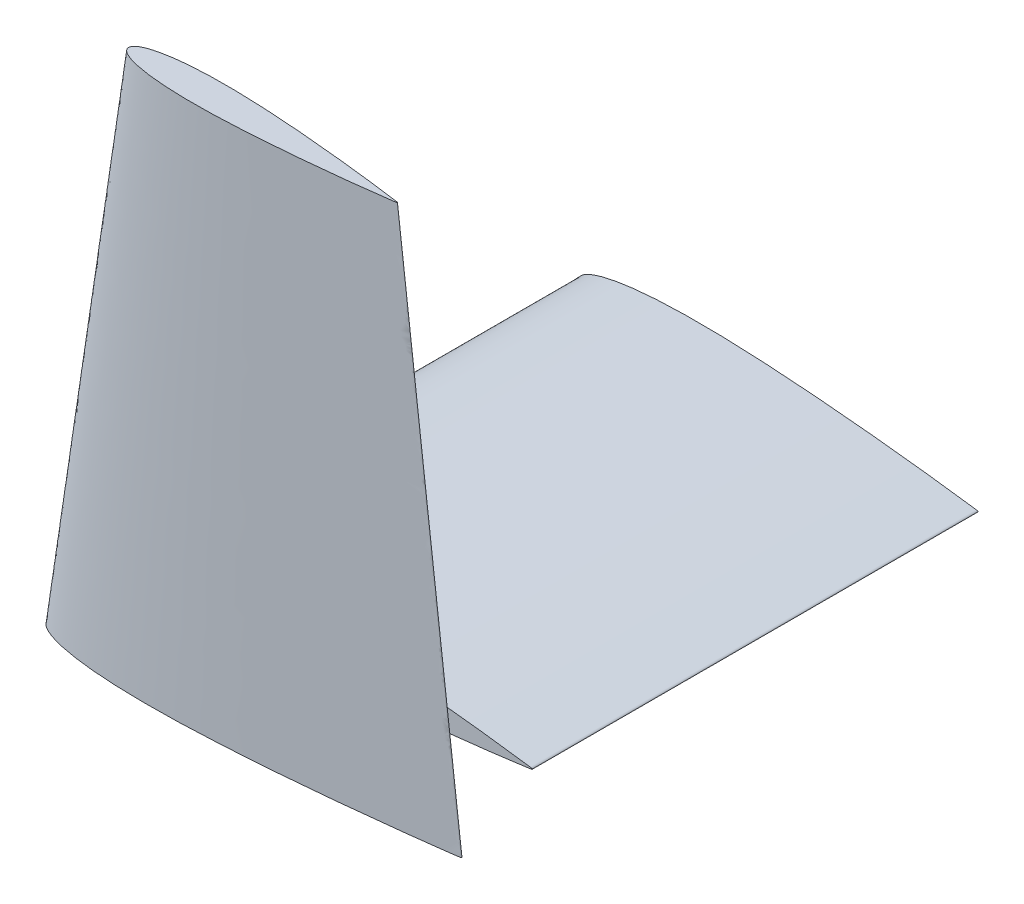
SolidWorks part; units mm, degrees
ref_plane "Front Plane" through (0, 0, 0) normal (0, 0, 1) x (1, 0, 0)
ref_plane "Top Plane" through (0, 0, 0) normal (0, 1, 0) x (1, 0, 0)
ref_plane "Right Plane" through (0, 0, 0) normal (1, 0, 0) x (0, 0, -1)
ref_plane "Plane1" through (0, 0, -61.341) normal (0, 0, 1) x (1, 0, 0)
sketch "Sketch2" plane through (0, 0, -61.341) normal (0, 0, 1) x (1, 0, 0)
  spline S1 degree 3 poles (318.9616, -0.5388) (318.9616, 0.5388) (317.8871, 0.4072) (316.5257, 0.7904) (314.029, 1.0273) (310.6656, 1.5357) (306.333, 2.103) (301.1081, 2.8022) (295.0047, 3.5926) (288.0667, 4.4725) (280.3349, 5.4267) (271.8575, 6.4421) (262.6867, 7.5062) (252.8789, 8.6045) (242.4947, 9.7236) (231.5982, 10.8496) (220.2564, 11.9679) (208.5394, 13.0629) (196.5193, 14.1202) (184.2704, 15.122) (171.8679, 16.0521) (159.3884, 16.8933) (146.9087, 17.6278) (134.5058, 18.2372) (122.2562, 18.7052) (110.2351, 19.0165) (98.5168, 19.156) (87.1732, 19.1125) (76.2743, 18.8777) (65.8873, 18.4456) (56.076, 17.8151) (46.9007, 16.9881) (38.4176, 15.971) (30.6784, 14.7725) (23.73, 13.4051) (17.6131, 11.8842) (12.3624, 10.2248) (8.0047, 8.4423) (4.5539, 6.5486) (2.0152, 4.5401) (0.3892, 2.3682) (-0.1814, 0) (0.3892, -2.3682) (2.0152, -4.5401) (4.5539, -6.5486) (8.0047, -8.4423) (12.3624, -10.2248) (17.6131, -11.8842) (23.73, -13.4051) (30.6784, -14.7725) (38.4176, -15.971) (46.9007, -16.9881) (56.076, -17.8151) (65.8873, -18.4456) (76.2743, -18.8777) (87.1732, -19.1125) (98.5168, -19.156) (110.2351, -19.0165) (122.2562, -18.7052) (134.5058, -18.2372) (146.9087, -17.6278) (159.3884, -16.8933) (171.8679, -16.0521) (184.2704, -15.122) (196.5193, -14.1202) (208.5394, -13.0629) (220.2564, -11.9679) (231.5982, -10.8496) (242.4947, -9.7236) (252.8789, -8.6045) (262.6867, -7.5062) (271.8575, -6.4421) (280.3349, -5.4267) (288.0667, -4.4725) (295.0047, -3.5926) (301.1081, -2.8022) (306.333, -2.103) (310.6656, -1.5357) (314.029, -1.0273) (316.5257, -0.7904) (317.8871, -0.4072) (318.9616, -0.5388) (318.9616, 0.5388) (317.8871, 0.4072) knots -0.004279 -0.001997 -0.001234 0 0.000762 0.003045 0.006832 0.012101 0.018818 0.026939 0.036415 0.047185 0.05918 0.072328 0.086544 0.101741 0.117823 0.134691 0.15224 0.170361 0.188941 0.207865 0.227016 0.246276 0.265525 0.284645 0.30352 0.322035 0.340078 0.357543 0.374325 0.39033 0.405464 0.419644 0.432793 0.444844 0.455738 0.465429 0.473886 0.481102 0.487102 0.491975 0.495931 0.499383 0.502835 0.50679 0.511664 0.517664 0.524879 0.533337 0.543028 0.553922 0.565972 0.579122 0.593302 0.608436 0.62444 0.641223 0.658687 0.676731 0.695245 0.714121 0.733241 0.75249 0.77175 0.7909 0.809825 0.828404 0.846525 0.864074 0.880942 0.897025 0.912222 0.926438 0.939585 0.951581 0.962351 0.971826 0.979948 0.986664 0.991933 0.995721 0.998003 0.998766 1 1.000762 1.003045 1.006832 only from (318.77, 0.4017) to (318.77, 0.4017)
  spline S2 degree 3 poles (318.9616, -0.5388) (318.9616, 0.5388) (317.8871, 0.4072) (316.5257, 0.7904) (314.029, 1.0273) (310.6656, 1.5357) (306.333, 2.103) (301.1081, 2.8022) (295.0047, 3.5926) (288.0667, 4.4725) (280.3349, 5.4267) (271.8575, 6.4421) (262.6867, 7.5062) (252.8789, 8.6045) (242.4947, 9.7236) (231.5982, 10.8496) (220.2564, 11.9679) (208.5394, 13.0629) (196.5193, 14.1202) (184.2704, 15.122) (171.8679, 16.0521) (159.3884, 16.8933) (146.9087, 17.6278) (134.5058, 18.2372) (122.2562, 18.7052) (110.2351, 19.0165) (98.5168, 19.156) (87.1732, 19.1125) (76.2743, 18.8777) (65.8873, 18.4456) (56.076, 17.8151) (46.9007, 16.9881) (38.4176, 15.971) (30.6784, 14.7725) (23.73, 13.4051) (17.6131, 11.8842) (12.3624, 10.2248) (8.0047, 8.4423) (4.5539, 6.5486) (2.0152, 4.5401) (0.3892, 2.3682) (-0.1814, 0) (0.3892, -2.3682) (2.0152, -4.5401) (4.5539, -6.5486) (8.0047, -8.4423) (12.3624, -10.2248) (17.6131, -11.8842) (23.73, -13.4051) (30.6784, -14.7725) (38.4176, -15.971) (46.9007, -16.9881) (56.076, -17.8151) (65.8873, -18.4456) (76.2743, -18.8777) (87.1732, -19.1125) (98.5168, -19.156) (110.2351, -19.0165) (122.2562, -18.7052) (134.5058, -18.2372) (146.9087, -17.6278) (159.3884, -16.8933) (171.8679, -16.0521) (184.2704, -15.122) (196.5193, -14.1202) (208.5394, -13.0629) (220.2564, -11.9679) (231.5982, -10.8496) (242.4947, -9.7236) (252.8789, -8.6045) (262.6867, -7.5062) (271.8575, -6.4421) (280.3349, -5.4267) (288.0667, -4.4725) (295.0047, -3.5926) (301.1081, -2.8022) (306.333, -2.103) (310.6656, -1.5357) (314.029, -1.0273) (316.5257, -0.7904) (317.8871, -0.4072) (318.9616, -0.5388) (318.9616, 0.5388) (317.8871, 0.4072) knots -0.004279 -0.001997 -0.001234 0 0.000762 0.003045 0.006832 0.012101 0.018818 0.026939 0.036415 0.047185 0.05918 0.072328 0.086544 0.101741 0.117823 0.134691 0.15224 0.170361 0.188941 0.207865 0.227016 0.246276 0.265525 0.284645 0.30352 0.322035 0.340078 0.357543 0.374325 0.39033 0.405464 0.419644 0.432793 0.444844 0.455738 0.465429 0.473886 0.481102 0.487102 0.491975 0.495931 0.499383 0.502835 0.50679 0.511664 0.517664 0.524879 0.533337 0.543028 0.553922 0.565972 0.579122 0.593302 0.608436 0.62444 0.641223 0.658687 0.676731 0.695245 0.714121 0.733241 0.75249 0.77175 0.7909 0.809825 0.828404 0.846525 0.864074 0.880942 0.897025 0.912222 0.926438 0.939585 0.951581 0.962351 0.971826 0.979948 0.986664 0.991933 0.995721 0.998003 0.998766 1 1.000762 1.003045 1.006832 only from (318.77, 0.4017) to (318.77, 0.4017)
  dimension "D1" = 0
extrude "Boss-Extrude1" add sketch "Sketch2" along normal blind 355.6
ref_plane "Plane2" through (0, -60.96, 0) normal (0, 1, 0) x (1, 0, 0)
sketch "Sketch3" plane through (0, -60.96, 0) normal (0, 1, 0) x (1, 0, 0)
  spline S1 degree 3 poles (291.0277, -323.1359) (291.0277, -322.0241) (289.919, -322.1598) (288.5142, -321.7644) (285.9379, -321.5199) (282.4673, -320.9954) (277.9966, -320.41) (272.6052, -319.6885) (266.3072, -318.8729) (259.1481, -317.9649) (251.1699, -316.9804) (242.4223, -315.9326) (232.9592, -314.8345) (222.8388, -313.7012) (212.1237, -312.5465) (200.8798, -311.3846) (189.1766, -310.2306) (177.0861, -309.1008) (164.6829, -308.0098) (152.0436, -306.976) (139.2458, -306.0162) (126.3685, -305.1483) (113.4911, -304.3903) (100.6929, -303.7615) (88.0528, -303.2786) (75.6486, -302.9574) (63.5567, -302.8135) (51.8516, -302.8583) (40.6054, -303.1006) (29.8873, -303.5465) (19.7633, -304.1971) (10.2955, -305.0505) (1.5421, -306.1) (-6.4438, -307.3367) (-13.6137, -308.7477) (-19.9256, -310.317) (-25.3436, -312.0293) (-29.8401, -313.8687) (-33.401, -315.8227) (-36.0206, -317.8952) (-37.6984, -320.1363) (-38.2872, -322.58) (-37.6984, -325.0237) (-36.0206, -327.2648) (-33.401, -329.3373) (-29.8401, -331.2913) (-25.3436, -333.1307) (-19.9256, -334.843) (-13.6137, -336.4123) (-6.4438, -337.8233) (1.5421, -339.06) (10.2955, -340.1095) (19.7633, -340.9629) (29.8873, -341.6135) (40.6054, -342.0594) (51.8516, -342.3017) (63.5567, -342.3465) (75.6486, -342.2026) (88.0528, -341.8814) (100.6929, -341.3985) (113.4911, -340.7697) (126.3685, -340.0117) (139.2458, -339.1438) (152.0436, -338.184) (164.6829, -337.1502) (177.0861, -336.0592) (189.1766, -334.9294) (200.8798, -333.7754) (212.1237, -332.6135) (222.8388, -331.4588) (232.9592, -330.3255) (242.4223, -329.2274) (251.1699, -328.1796) (259.1481, -327.1951) (266.3072, -326.2871) (272.6052, -325.4715) (277.9966, -324.75) (282.4673, -324.1646) (285.9379, -323.6401) (288.5142, -323.3956) (289.919, -323.0002) (291.0277, -323.1359) (291.0277, -322.0241) (289.919, -322.1598) knots -0.004279 -0.001997 -0.001234 0 0.000762 0.003045 0.006832 0.012101 0.018818 0.026939 0.036415 0.047185 0.05918 0.072328 0.086544 0.101741 0.117823 0.134691 0.15224 0.170361 0.188941 0.207865 0.227016 0.246276 0.265525 0.284645 0.30352 0.322035 0.340078 0.357543 0.374325 0.39033 0.405464 0.419644 0.432793 0.444844 0.455738 0.465429 0.473886 0.481102 0.487102 0.491975 0.495931 0.499383 0.502835 0.50679 0.511664 0.517664 0.524879 0.533337 0.543028 0.553922 0.565972 0.579122 0.593302 0.608436 0.62444 0.641223 0.658687 0.676731 0.695245 0.714121 0.733241 0.75249 0.77175 0.7909 0.809825 0.828404 0.846525 0.864074 0.880942 0.897025 0.912222 0.926438 0.939585 0.951581 0.962351 0.971826 0.979948 0.986664 0.991933 0.995721 0.998003 0.998766 1 1.000762 1.003045 1.006832 only from (290.83, -322.1655) to (290.83, -322.1655)
  spline S2 degree 3 poles (291.0277, -323.1359) (291.0277, -322.0241) (289.919, -322.1598) (288.5142, -321.7644) (285.9379, -321.5199) (282.4673, -320.9954) (277.9966, -320.41) (272.6052, -319.6885) (266.3072, -318.8729) (259.1481, -317.9649) (251.1699, -316.9804) (242.4223, -315.9326) (232.9592, -314.8345) (222.8388, -313.7012) (212.1237, -312.5465) (200.8798, -311.3846) (189.1766, -310.2306) (177.0861, -309.1008) (164.6829, -308.0098) (152.0436, -306.976) (139.2458, -306.0162) (126.3685, -305.1483) (113.4911, -304.3903) (100.6929, -303.7615) (88.0528, -303.2786) (75.6486, -302.9574) (63.5567, -302.8135) (51.8516, -302.8583) (40.6054, -303.1006) (29.8873, -303.5465) (19.7633, -304.1971) (10.2955, -305.0505) (1.5421, -306.1) (-6.4438, -307.3367) (-13.6137, -308.7477) (-19.9256, -310.317) (-25.3436, -312.0293) (-29.8401, -313.8687) (-33.401, -315.8227) (-36.0206, -317.8952) (-37.6984, -320.1363) (-38.2872, -322.58) (-37.6984, -325.0237) (-36.0206, -327.2648) (-33.401, -329.3373) (-29.8401, -331.2913) (-25.3436, -333.1307) (-19.9256, -334.843) (-13.6137, -336.4123) (-6.4438, -337.8233) (1.5421, -339.06) (10.2955, -340.1095) (19.7633, -340.9629) (29.8873, -341.6135) (40.6054, -342.0594) (51.8516, -342.3017) (63.5567, -342.3465) (75.6486, -342.2026) (88.0528, -341.8814) (100.6929, -341.3985) (113.4911, -340.7697) (126.3685, -340.0117) (139.2458, -339.1438) (152.0436, -338.184) (164.6829, -337.1502) (177.0861, -336.0592) (189.1766, -334.9294) (200.8798, -333.7754) (212.1237, -332.6135) (222.8388, -331.4588) (232.9592, -330.3255) (242.4223, -329.2274) (251.1699, -328.1796) (259.1481, -327.1951) (266.3072, -326.2871) (272.6052, -325.4715) (277.9966, -324.75) (282.4673, -324.1646) (285.9379, -323.6401) (288.5142, -323.3956) (289.919, -323.0002) (291.0277, -323.1359) (291.0277, -322.0241) (289.919, -322.1598) knots -0.004279 -0.001997 -0.001234 0 0.000762 0.003045 0.006832 0.012101 0.018818 0.026939 0.036415 0.047185 0.05918 0.072328 0.086544 0.101741 0.117823 0.134691 0.15224 0.170361 0.188941 0.207865 0.227016 0.246276 0.265525 0.284645 0.30352 0.322035 0.340078 0.357543 0.374325 0.39033 0.405464 0.419644 0.432793 0.444844 0.455738 0.465429 0.473886 0.481102 0.487102 0.491975 0.495931 0.499383 0.502835 0.50679 0.511664 0.517664 0.524879 0.533337 0.543028 0.553922 0.565972 0.579122 0.593302 0.608436 0.62444 0.641223 0.658687 0.676731 0.695245 0.714121 0.733241 0.75249 0.77175 0.7909 0.809825 0.828404 0.846525 0.864074 0.880942 0.897025 0.912222 0.926438 0.939585 0.951581 0.962351 0.971826 0.979948 0.986664 0.991933 0.995721 0.998003 0.998766 1 1.000762 1.003045 1.006832 only from (290.83, -322.1655) to (290.83, -322.1655)
  dimension "D1" = 0
ref_plane "Plane3" through (0, 365.76, 0) normal (0, -1, 0) x (-1, 0, 0)
sketch "Sketch4" plane through (0, 365.76, 0) normal (0, -1, 0) x (-1, 0, 0)
  spline S1 degree 3 poles (-238.929, -322.3065) (-239.6507, -322.2181) (-239.6507, -322.9419) (-238.929, -322.8535) (-238.0145, -323.1109) (-236.3374, -323.2701) (-234.0782, -323.6115) (-231.1679, -323.9926) (-227.6583, -324.4623) (-223.5585, -324.9932) (-218.8982, -325.5843) (-213.7046, -326.2252) (-208.0103, -326.9073) (-201.8501, -327.622) (-195.2621, -328.3598) (-188.2869, -329.1115) (-180.9675, -329.8678) (-173.3491, -330.619) (-165.4787, -331.3545) (-157.4046, -332.0647) (-149.1769, -332.7377) (-140.8459, -333.3624) (-132.4633, -333.9274) (-124.0805, -334.4208) (-115.7493, -334.8302) (-107.5211, -335.1445) (-99.4464, -335.3537) (-91.575, -335.4473) (-83.9554, -335.4181) (-76.6345, -335.2604) (-69.6574, -334.9702) (-63.067, -334.5466) (-56.9038, -333.9911) (-51.2056, -333.3079) (-46.0071, -332.5029) (-41.3397, -331.5844) (-37.2309, -330.5628) (-33.704, -329.4481) (-30.7769, -328.2508) (-28.4589, -326.9788) (-26.7536, -325.6297) (-25.6614, -324.1708) (-25.2782, -322.58) (-25.6614, -320.9892) (-26.7536, -319.5303) (-28.4589, -318.1812) (-30.7769, -316.9092) (-33.704, -315.7119) (-37.2309, -314.5972) (-41.3397, -313.5756) (-46.0071, -312.6571) (-51.2056, -311.8521) (-56.9038, -311.1689) (-63.067, -310.6134) (-69.6574, -310.1898) (-76.6345, -309.8996) (-83.9554, -309.7419) (-91.575, -309.7127) (-99.4464, -309.8063) (-107.5211, -310.0155) (-115.7493, -310.3298) (-124.0805, -310.7392) (-132.4633, -311.2326) (-140.8459, -311.7976) (-149.1769, -312.4223) (-157.4046, -313.0953) (-165.4787, -313.8055) (-173.3491, -314.541) (-180.9675, -315.2922) (-188.2869, -316.0485) (-195.2621, -316.8002) (-201.8501, -317.538) (-208.0103, -318.2527) (-213.7046, -318.9348) (-218.8982, -319.5757) (-223.5585, -320.1668) (-227.6583, -320.6977) (-231.1679, -321.1674) (-234.0782, -321.5485) (-236.3374, -321.8899) (-238.0145, -322.0491) (-238.929, -322.3065) (-239.6507, -322.2181) (-239.6507, -322.9419) knots -0.006832 -0.003045 -0.000762 0 0.001234 0.001997 0.004279 0.008067 0.013336 0.020052 0.028174 0.037649 0.048419 0.060415 0.073562 0.087778 0.102975 0.119058 0.135926 0.153475 0.171596 0.190175 0.2091 0.22825 0.24751 0.266759 0.285879 0.304755 0.323269 0.341313 0.358777 0.37556 0.391564 0.406698 0.420878 0.434028 0.446078 0.456972 0.466663 0.475121 0.482336 0.488336 0.49321 0.497165 0.500617 0.504069 0.508025 0.512898 0.518898 0.526114 0.534571 0.544262 0.555156 0.567207 0.580356 0.594536 0.60967 0.625675 0.642457 0.659922 0.677965 0.69648 0.715355 0.734475 0.753724 0.772984 0.792135 0.811059 0.829639 0.84776 0.865309 0.882177 0.898259 0.913456 0.927672 0.94082 0.952815 0.963585 0.973061 0.981182 0.987899 0.993168 0.996955 0.999238 1 1.001234 1.001997 1.004279 only from (-239.522, -322.3102) to (-239.522, -322.3102)
  spline S2 degree 3 poles (-238.929, -322.3065) (-239.6507, -322.2181) (-239.6507, -322.9419) (-238.929, -322.8535) (-238.0145, -323.1109) (-236.3374, -323.2701) (-234.0782, -323.6115) (-231.1679, -323.9926) (-227.6583, -324.4623) (-223.5585, -324.9932) (-218.8982, -325.5843) (-213.7046, -326.2252) (-208.0103, -326.9073) (-201.8501, -327.622) (-195.2621, -328.3598) (-188.2869, -329.1115) (-180.9675, -329.8678) (-173.3491, -330.619) (-165.4787, -331.3545) (-157.4046, -332.0647) (-149.1769, -332.7377) (-140.8459, -333.3624) (-132.4633, -333.9274) (-124.0805, -334.4208) (-115.7493, -334.8302) (-107.5211, -335.1445) (-99.4464, -335.3537) (-91.575, -335.4473) (-83.9554, -335.4181) (-76.6345, -335.2604) (-69.6574, -334.9702) (-63.067, -334.5466) (-56.9038, -333.9911) (-51.2056, -333.3079) (-46.0071, -332.5029) (-41.3397, -331.5844) (-37.2309, -330.5628) (-33.704, -329.4481) (-30.7769, -328.2508) (-28.4589, -326.9788) (-26.7536, -325.6297) (-25.6614, -324.1708) (-25.2782, -322.58) (-25.6614, -320.9892) (-26.7536, -319.5303) (-28.4589, -318.1812) (-30.7769, -316.9092) (-33.704, -315.7119) (-37.2309, -314.5972) (-41.3397, -313.5756) (-46.0071, -312.6571) (-51.2056, -311.8521) (-56.9038, -311.1689) (-63.067, -310.6134) (-69.6574, -310.1898) (-76.6345, -309.8996) (-83.9554, -309.7419) (-91.575, -309.7127) (-99.4464, -309.8063) (-107.5211, -310.0155) (-115.7493, -310.3298) (-124.0805, -310.7392) (-132.4633, -311.2326) (-140.8459, -311.7976) (-149.1769, -312.4223) (-157.4046, -313.0953) (-165.4787, -313.8055) (-173.3491, -314.541) (-180.9675, -315.2922) (-188.2869, -316.0485) (-195.2621, -316.8002) (-201.8501, -317.538) (-208.0103, -318.2527) (-213.7046, -318.9348) (-218.8982, -319.5757) (-223.5585, -320.1668) (-227.6583, -320.6977) (-231.1679, -321.1674) (-234.0782, -321.5485) (-236.3374, -321.8899) (-238.0145, -322.0491) (-238.929, -322.3065) (-239.6507, -322.2181) (-239.6507, -322.9419) knots -0.006832 -0.003045 -0.000762 0 0.001234 0.001997 0.004279 0.008067 0.013336 0.020052 0.028174 0.037649 0.048419 0.060415 0.073562 0.087778 0.102975 0.119058 0.135926 0.153475 0.171596 0.190175 0.2091 0.22825 0.24751 0.266759 0.285879 0.304755 0.323269 0.341313 0.358777 0.37556 0.391564 0.406698 0.420878 0.434028 0.446078 0.456972 0.466663 0.475121 0.482336 0.488336 0.49321 0.497165 0.500617 0.504069 0.508025 0.512898 0.518898 0.526114 0.534571 0.544262 0.555156 0.567207 0.580356 0.594536 0.60967 0.625675 0.642457 0.659922 0.677965 0.69648 0.715355 0.734475 0.753724 0.772984 0.792135 0.811059 0.829639 0.84776 0.865309 0.882177 0.898259 0.913456 0.927672 0.94082 0.952815 0.963585 0.973061 0.981182 0.987899 0.993168 0.996955 0.999238 1 1.001234 1.001997 1.004279 only from (-239.522, -322.3102) to (-239.522, -322.3102)
  dimension "D1" = 0
loft "Loft1" add profiles "Sketch3", "Sketch4"
